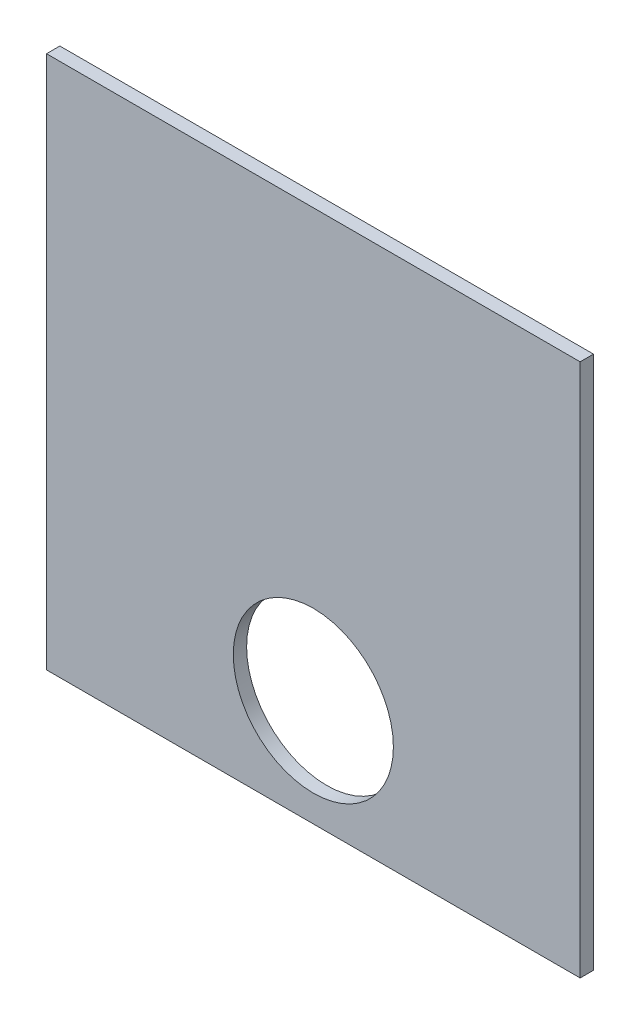
SolidWorks part; units mm, degrees
ref_plane "Front Plane" through (0, 0, 0) normal (0, 0, 1) x (1, 0, 0)
ref_plane "Top Plane" through (0, 0, 0) normal (0, 1, 0) x (1, 0, 0)
ref_plane "Right Plane" through (0, 0, 0) normal (1, 0, 0) x (0, 0, -1)
sketch "Sketch1" plane through (0, 0, 0) normal (0, 0, 1) x (1, 0, 0)
  line L1 (0, 0) -> (254, 0)
  line L2 (0, 0) -> (0, 254)
  line L3 (0, 254) -> (254, 254)
  line L4 (254, 0) -> (254, 254)
  dimension "D1" = 254
  dimension "D2" = 254
extrude "Boss-Extrude1" add sketch "Sketch1" along normal blind 6.35 contours L3 L4 L1 L2
sketch "Sketch2" plane through (0, 0, 6.35) normal (0, 0, 1) x (1, 0, 0)
  line L0 (127, 50.8) -> (127, 0) construction
  line L1 (0, 0) -> (254, 0) construction
  circle A0 centre (127, 50.8) radius 38.1
  dimension "D1" = 76.2
  dimension "D2" = 50.8
extrude "Cut-Extrude1" cut sketch "Sketch2" against normal through all
